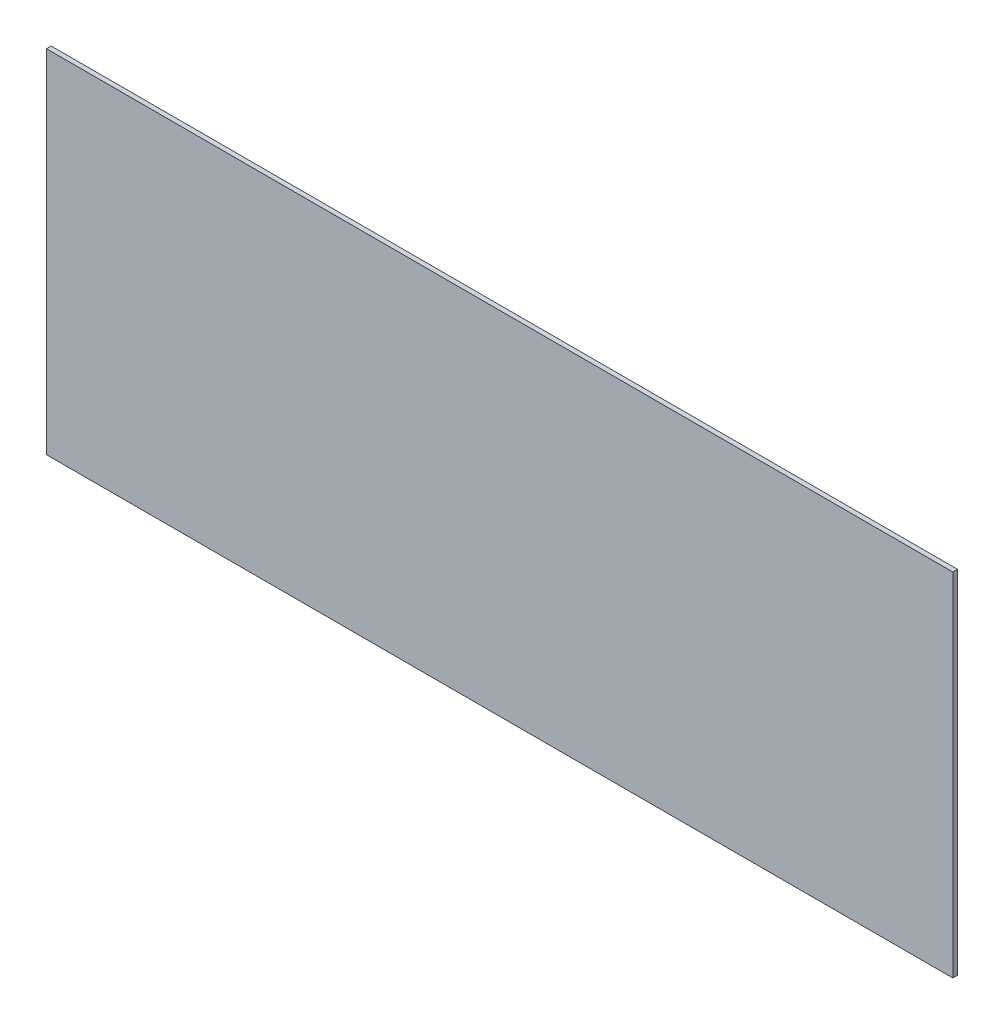
SolidWorks part; units mm, degrees
ref_plane "前基準面" through (0, 0, 0) normal (0, 0, 1) x (1, 0, 0)
ref_plane "上基準面" through (0, 0, 0) normal (0, 1, 0) x (1, 0, 0)
ref_plane "右基準面" through (0, 0, 0) normal (1, 0, 0) x (0, 0, -1)
sketch "草圖1" plane through (0, 0, 0) normal (0, 0, 1) x (1, 0, 0)
  line L1 (-151.6472, 64.9097) -> (138.3528, 64.9097)
  line L2 (-151.6472, 64.9097) -> (-151.6472, -47.5903)
  line L3 (-151.6472, -47.5903) -> (138.3528, -47.5903)
  line L4 (138.3528, 64.9097) -> (138.3528, -47.5903)
  dimension "D1" = 290
  dimension "D2" = 112.5
extrude "填料-伸長1" add sketch "草圖1" along normal blind 1.5
